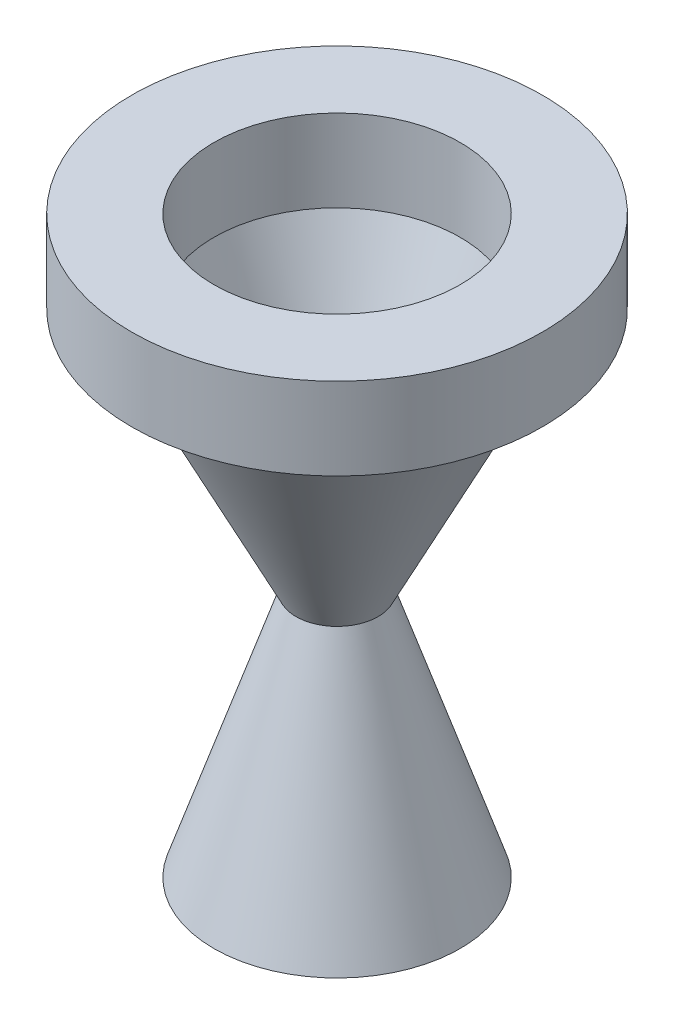
SolidWorks part; units mm, degrees
ref_plane "Front Plane" through (0, 0, 0) normal (0, 0, 1) x (1, 0, 0)
ref_plane "Top Plane" through (0, 0, 0) normal (0, 1, 0) x (1, 0, 0)
ref_plane "Right Plane" through (0, 0, 0) normal (1, 0, 0) x (0, 0, -1)
sketch "Sketch1" plane through (0, 0, 0) normal (0, 1, 0) x (1, 0, 0)
  circle A0 centre (0, 0) radius 63.5
  circle A1 centre (0, 0) radius 38.1
  dimension "D1" = 127
  dimension "D2" = 76.2
extrude "Boss-Extrude1" add sketch "Sketch1" along normal blind 25.4
sketch "Sketch2" plane through (0, 0, 0) normal (0, 1, 0) x (1, 0, 0)
  circle A0 centre (0, 0) radius 38.1
  circle A1 centre (0, 0) radius 50.8
  dimension "D1" = 101.6
ref_plane "Plane1" through (0, -76.2, 0) normal (0, 1, 0) x (1, 0, 0)
sketch "Sketch3" plane through (0, -76.2, 0) normal (0, 1, 0) x (1, 0, 0)
  circle A0 centre (0, 0) radius 6.35
  circle A1 centre (0, 0) radius 12.7
  dimension "D1" = 12.7
  dimension "D2" = 25.4
sketch "Sketch4" plane through (0, 0, 0) normal (0, 0, 1) x (1, 0, 0)
  line L0 (50.8, 0) -> (12.7, -76.2)
  line L1 (50.8, 0) -> (-50.8, 0) construction
  line L2 (12.7, -76.2) -> (-12.7, -76.2) construction
  line L3 (38.1, 0) -> (6.35, -76.2)
  line L4 (38.1, 0) -> (-38.1, 0) construction
  line L5 (6.35, -76.2) -> (-6.35, -76.2) construction
  line L6 (50.8, 0) -> (38.1, 0)
  line L7 (12.7, -76.2) -> (6.35, -76.2)
  line L8 (0, -76.2) -> (0, 0) construction
revolve "Revolve1" add sketch "Sketch4" angle 360 about L8
ref_plane "Plane2" through (0, -152.4, 0) normal (0, 1, 0) x (1, 0, 0)
sketch "Sketch5" plane through (0, -152.4, 0) normal (0, 1, 0) x (1, 0, 0)
  circle A0 centre (0, 0) radius 25.4
  circle A1 centre (0, 0) radius 38.1
  dimension "D1" = 50.8
  dimension "D2" = 76.2
sketch "Sketch6" plane through (0, 0, 0) normal (0, 0, 1) x (1, 0, 0)
  line L0 (12.7, -76.2) -> (38.1, -152.4)
  line L1 (38.1, -152.4) -> (-38.1, -152.4) construction
  line L2 (6.35, -76.2) -> (25.4, -152.4)
  line L3 (6.35, -76.2) -> (-6.35, -76.2) construction
  line L4 (12.7, -76.2) -> (-12.7, -76.2) construction
  line L5 (25.4, -152.4) -> (-25.4, -152.4) construction
  line L6 (25.4, -152.4) -> (38.1, -152.4)
  line L7 (12.7, -76.2) -> (6.35, -76.2)
  line L8 (0, -76.2) -> (0, -152.4) construction
revolve "Revolve2" add sketch "Sketch6" angle 360 about L8
fillet "Fillet1" radius 5.08 1 edges at (0, -76.2, 6.35)
